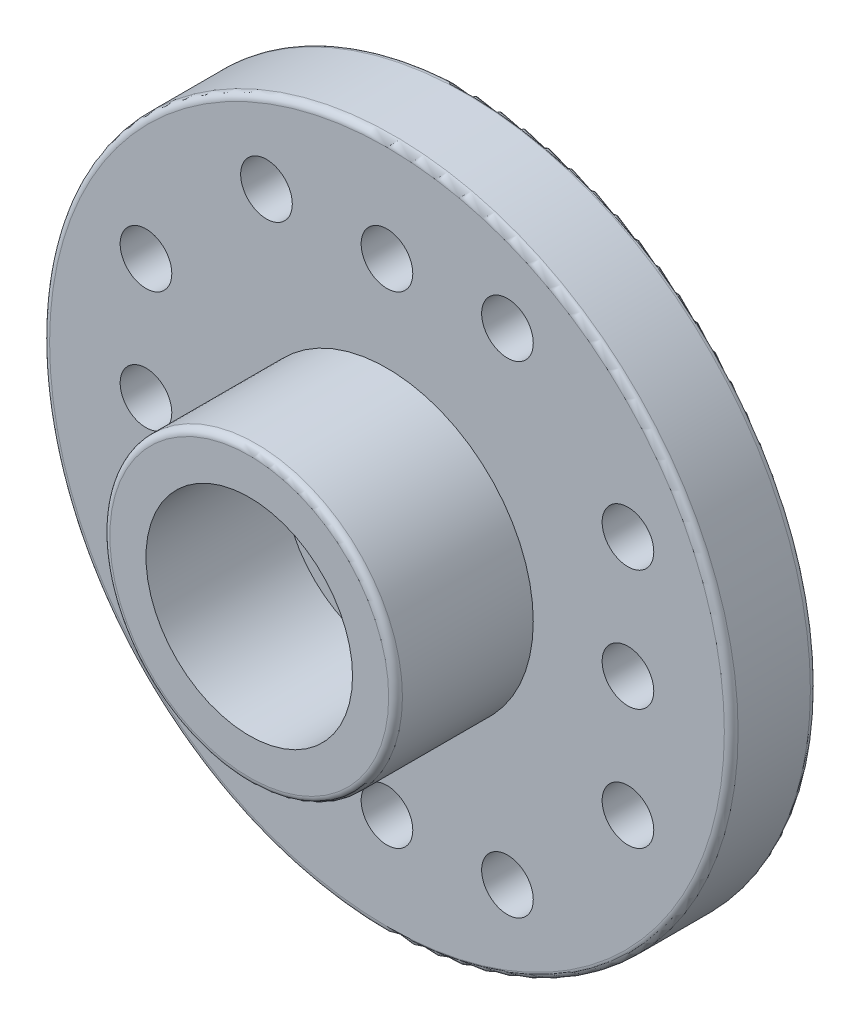
SolidWorks part; units mm, degrees
material "PE High Density Film"
ref_plane "Front Plane" through (0, 0, 0) normal (0, 0, 1) x (1, 0, 0)
ref_plane "Top Plane" through (0, 0, 0) normal (0, 1, 0) x (1, 0, 0)
ref_plane "Right Plane" through (0, 0, 0) normal (1, 0, 0) x (0, 0, -1)
sketch "Sketch1" plane through (0, 0, 0) normal (0, 0, 1) x (1, 0, 0)
  line L0 (-7, 3.5) -> (-7, -3.5) construction
  line L1 (-7, 0) -> (0, 0) construction
  circle A0 centre (0, 0) radius 10
  circle A1 centre (-7, 0) radius 0.75
  circle A2 centre (3.5, 7) radius 0.75
  circle A3 centre (0, 7) radius 0.75
  circle A4 centre (-3.5, 7) radius 0.75
  circle A5 centre (7, -3.5) radius 0.75
  circle A6 centre (7, 0) radius 0.75
  circle A7 centre (7, 3.5) radius 0.75
  circle A8 centre (-3.5, -7) radius 0.75
  circle A9 centre (0, -7) radius 0.75
  circle A10 centre (3.5, -7) radius 0.75
  circle A11 centre (-7, -3.5) radius 0.75
  circle A13 centre (-7, 3.5) radius 0.75
  circle A22 centre (0, 0) radius 1.5
  point P25 (0, 0)
  dimension "D2" = 20
  dimension "D4" = 7
  dimension "D5" = 3.5
  dimension "D14" = 3
  dimension "D6" = 3.5
  dimension "D3" = 1.5
extrude "Boss-Extrude1" add sketch "Sketch1" along normal blind 2.5
sketch "Sketch5" plane through (0, 0, 2.5) normal (0, 0, 1) x (1, 0, 0)
  circle A0 centre (0, 0) radius 3
  circle A1 centre (0, 0) radius 4.25
  dimension "D1" = 8.5
extrude "Boss-Extrude2" add sketch "Sketch5" along normal blind 4
sketch "Sketch6" plane through (0, 0, 0) normal (0, 0, -1) x (-1, 0, 0)
  circle A0 centre (0, 0) radius 4.5
  dimension "D1" = 9
extrude "Cut-Extrude1" cut sketch "Sketch6" against normal blind 0.8
sketch "Sketch7" plane through (0, 0, 0.8) normal (0, 0, -1) x (-1, 0, 0)
  circle A0 centre (0, 0) radius 3.5
  circle A1 centre (0, 0) radius 3.7
  dimension "D1" = 7
  dimension "D3" = 0
  dimension "D2" = 0.2
extrude "Boss-Extrude3" add sketch "Sketch7" along normal blind 0.8
fillet "Fillet1" radius 0.2 4 edges at (10, 0, 0) (10, 0, 2.5) (-4.5, 0, 0) (4.25, 0, 6.5)
